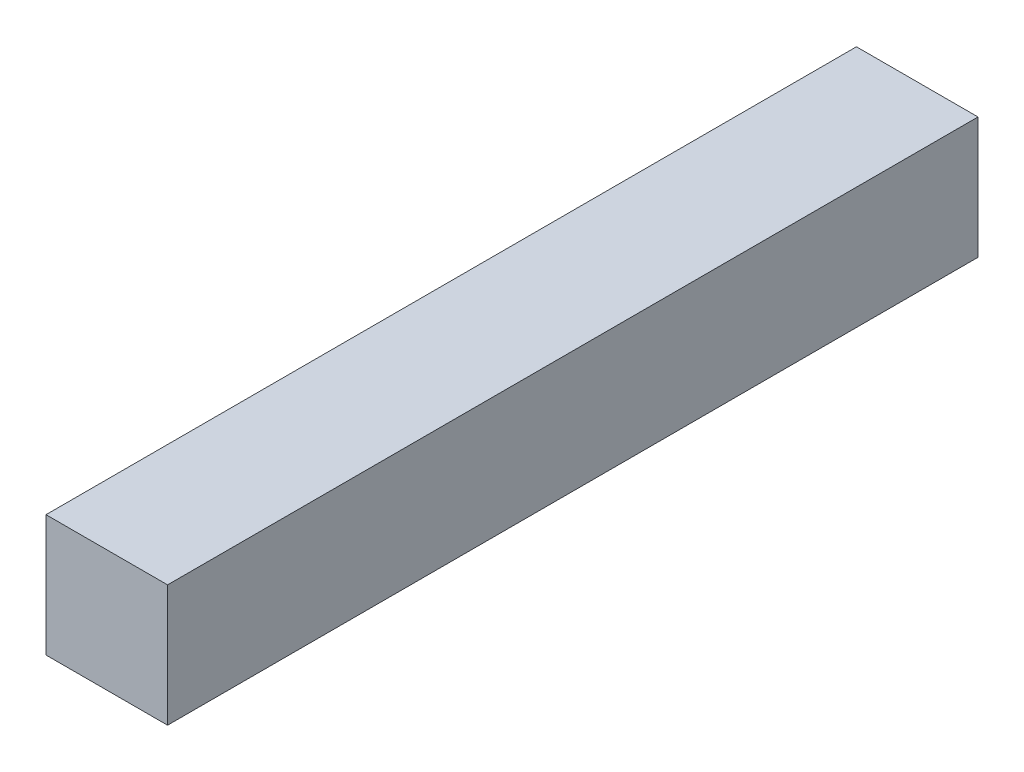
SolidWorks part; units mm, degrees
ref_plane "Front Plane" through (0, 0, 0) normal (0, 0, 1) x (1, 0, 0)
ref_plane "Top Plane" through (0, 0, 0) normal (0, 1, 0) x (1, 0, 0)
ref_plane "Right Plane" through (0, 0, 0) normal (1, 0, 0) x (0, 0, -1)
sketch "Sketch1" plane through (0, 0, 0) normal (0, 0, 1) x (1, 0, 0)
  line L1 (0, 0) -> (38.1, 0)
  line L2 (0, 0) -> (0, 38.1)
  line L3 (0, 38.1) -> (38.1, 38.1)
  line L4 (38.1, 0) -> (38.1, 38.1)
  dimension "D1" = 38.1
  dimension "D2" = 38.1
extrude "Boss-Extrude1" add sketch "Sketch1" along normal blind 254
